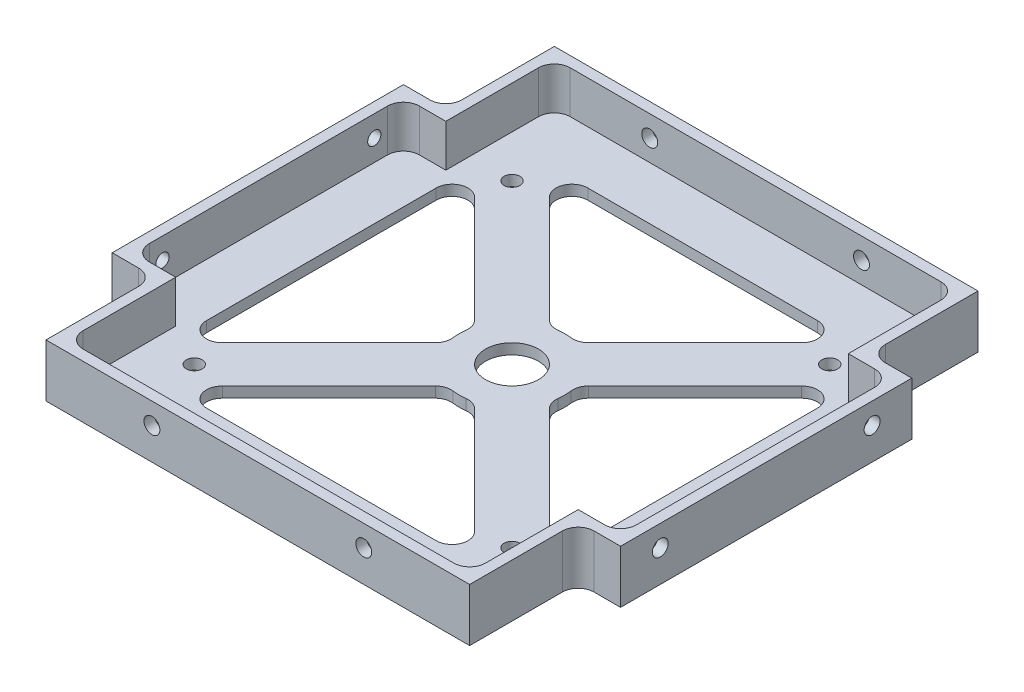
SolidWorks part; units mm, degrees
material "6061-T6 (SS)"
ref_plane "Front Plane" through (0, 0, 0) normal (0, 0, 1) x (1, 0, 0)
ref_plane "Top Plane" through (0, 0, 0) normal (0, 1, 0) x (1, 0, 0)
ref_plane "Right Plane" through (0, 0, 0) normal (1, 0, 0) x (0, 0, -1)
sketch "Sketch1" plane through (0, 0, 0) normal (0, 1, 0) x (1, 0, 0)
  line L0 (0, 8) -> (8, 0)
  line L1 (0, 0) -> (96, 0)
  line L2 (0, 0) -> (0, 96)
  line L3 (0, 96) -> (96, 96)
  line L4 (96, 0) -> (96, 96)
  line L5 (48, 96) -> (48, 0) construction
  line L6 (0, 48) -> (96, 48) construction
  line L7 (96, 8) -> (88, 0)
  line L8 (96, 88) -> (88, 96)
  line L9 (0, 88) -> (8, 96)
  dimension "D1" = 96
  dimension "D2" = 96
  dimension "D3" = 8
  dimension "D4" = 8
extrude "Boss-Extrude1" add sketch "Sketch1" along normal blind 10 contours L9 L2 L0 L1 L7 L4 L8 L3
sketch "Sketch2" plane through (0, 0, 0) normal (0, -1, 0) x (-1, 0, 0)
  line L0 (-4, 92) -> (-92, 4) construction
  line L1 (0, 88) -> (-8, 96) construction
  line L2 (-96, 8) -> (-88, 0) construction
  line L3 (-92, 92) -> (-4, 4) construction
  line L4 (-96, 88) -> (-88, 96) construction
  line L5 (0, 8) -> (-8, 0) construction
  line L6 (-12, 84) -> (-84, 84) construction
  line L7 (-84, 84) -> (-84, 12) construction
  line L8 (-84, 12) -> (-12, 12) construction
  line L9 (-12, 12) -> (-12, 84) construction
  line L10 (-8, 96) -> (-88, 96) construction
  line L12 (-19.0711, 84) -> (-84, 19.0711)
  line L13 (-12, 76.9289) -> (-76.9289, 12)
  line L14 (-12, 19.0711) -> (-76.9289, 84)
  line L15 (-19.0711, 12) -> (-84, 76.9289)
  line L16 (-12, 76.9289) -> (-12, 19.0711)
  line L17 (-19.0711, 12) -> (-76.9289, 12)
  line L18 (-84, 19.0711) -> (-84, 76.9289)
  line L19 (-76.9289, 84) -> (-19.0711, 84)
  circle A0 centre (-48, 48) radius 10
  circle A1 centre (-48, 48) radius 5
  dimension "D6" = 20
  dimension "D7" = 10
  dimension "D1" = 12
  dimension "D2" = 10
  dimension "D3" = 5
  dimension "D4" = 10
  dimension "D5" = 5
extrude "Cut-Extrude1" cut sketch "Sketch2" against normal through all contours A0 L12 L19 L14 | A0 L14 L16 L13 | A0 L13 L17 L15 | A0 L15 L18 L12 | A1
fillet "Fillet1" radius 3 16 edges at (19.0711, 5, -12) (76.9289, 5, -12) (50.5882, 5, -38.3407) (38.3407, 5, -50.5882) (45.4118, 5, -38.3407) (57.6593, 5, -50.5882) (12, 5, -19.0711) (38.3407, 5, -45.4118) (50.5882, 5, -57.6593) (84, 5, -19.0711) (84, 5, -76.9289) (57.6593, 5, -45.4118) (45.4118, 5, -57.6593) (76.9289, 5, -84) (19.0711, 5, -84) (12, 5, -76.9289)
sketch "Sketch5" plane through (0, 10, 0) normal (0, 1, 0) x (1, 0, 0)
  line L0 (8, 0) -> (8, 20.5)
  line L3 (0, 8) -> (8, 0)
  line L4 (0, 8) -> (0, 20.5)
  line L5 (0, 8) -> (0, 88) construction
  line L6 (0, 20.5) -> (8, 20.5)
  line L7 (0, 48) -> (96, 48) construction
  line L8 (96, 8) -> (96, 88) construction
  line L9 (48, 96) -> (48, 0) construction
  line L10 (8, 96) -> (88, 96) construction
  line L11 (8, 0) -> (88, 0) construction
  line L12 (96, 8) -> (88, 0)
  line L13 (96, 8) -> (96, 20.5)
  line L14 (96, 20.5) -> (88, 20.5)
  line L15 (88, 0) -> (88, 20.5)
  line L16 (96, 75.5) -> (88, 75.5)
  line L17 (96, 88) -> (96, 75.5)
  line L18 (96, 88) -> (88, 96)
  line L19 (88, 96) -> (88, 75.5)
  line L20 (8, 96) -> (8, 75.5)
  line L21 (0, 88) -> (8, 96)
  line L22 (0, 88) -> (0, 75.5)
  line L23 (0, 75.5) -> (8, 75.5)
  dimension "D1" = 20.5
extrude "Cut-Extrude4" cut sketch "Sketch5" against normal through all
sketch "Sketch6" plane through (0, 10, 0) normal (0, 1, 0) x (1, 0, 0)
  line L90 (86, 73.5) -> (86, 94)
  line L91 (94, 73.5) -> (86, 73.5)
  line L92 (94, 22.5) -> (94, 73.5)
  line L93 (86, 22.5) -> (94, 22.5)
  line L94 (86, 2) -> (86, 22.5)
  line L95 (10, 2) -> (86, 2)
  line L96 (10, 22.5) -> (10, 2)
  line L97 (2, 22.5) -> (10, 22.5)
  line L98 (2, 73.5) -> (2, 22.5)
  line L99 (10, 73.5) -> (2, 73.5)
  line L100 (10, 94) -> (10, 73.5)
  line L101 (86, 94) -> (10, 94)
  line L102 (86, 73.5) -> (86, 94)
  line L103 (94, 73.5) -> (86, 73.5)
  line L104 (94, 22.5) -> (94, 73.5)
  line L105 (86, 22.5) -> (94, 22.5)
  line L106 (86, 2) -> (86, 22.5)
  line L107 (10, 2) -> (86, 2)
  line L108 (10, 22.5) -> (10, 2)
  line L109 (2, 22.5) -> (10, 22.5)
  line L110 (2, 73.5) -> (2, 22.5)
  line L111 (10, 73.5) -> (2, 73.5)
  line L112 (10, 94) -> (10, 73.5)
  line L113 (86, 94) -> (10, 94)
  dimension "D1" = 2
extrude "Cut-Extrude5" cut sketch "Sketch6" against normal blind 8
fillet "Fillet2" radius 3 12 edges at (88, 5, -75.5) (88, 5, -20.5) (8, 5, -75.5) (8, 5, -20.5) (86, 6, -94) (94, 6, -73.5) (94, 6, -22.5) (86, 6, -2) (10, 6, -94) (10, 6, -2) (2, 6, -22.5) (2, 6, -73.5)
sketch "Sketch7" plane through (0, 0, 0) normal (0, -1, 0) x (1, 0, 0)
  line L0 (78, -18) -> (18, -18) construction
  line L1 (78, -78) -> (18, -78)
  line L2 (78, -78) -> (78, -18)
  line L3 (78, -18) -> (18, -18)
  line L4 (18, -78) -> (18, -18)
  line L5 (78, -78) -> (18, -18) construction
  line L6 (78, -18) -> (18, -78) construction
  line L7 (78, -18) -> (78, -78) construction
  line L8 (8, 0) -> (88, 0) construction
  line L9 (96, -20.5) -> (96, -75.5) construction
  line L10 (88, -96) -> (88, -78.5) construction
  circle A0 centre (78, -18) radius 1.5
  circle A1 centre (18, -18) radius 1.5
  circle A2 centre (18, -78) radius 1.5
  circle A3 centre (78, -78) radius 1.5
  point P0 (48, -48)
  dimension "D1" = 2
  dimension "D5" = 3
  dimension "D8" = 10
  dimension "D2" = 60
  dimension "D3" = 60
  dimension "D6" = 18
  dimension "D7" = 18
  dimension "D4" = 2
sketch "Sketch8" plane through (0, 0, 0) normal (0, 0, 1) x (1, 0, 0)
  line L0 (8, 6) -> (88, 6) construction
  line L1 (8, 10) -> (8, 0) construction
  line L2 (88, 10) -> (88, 0) construction
  line L3 (8, 0) -> (88, 0) construction
  line L4 (48, 10) -> (48, 0) construction
  line L5 (8, 10) -> (88, 10) construction
  dimension "D1" = 6
sketch "Sketch9" plane through (0, 0, 0) normal (-1, 0, 0) x (0, 0, 1)
  line L0 (-75.5, 6) -> (-20.5, 6) construction
  line L1 (-75.5, 0) -> (-75.5, 10) construction
  line L2 (-20.5, 0) -> (-20.5, 10) construction
  line L3 (-20.5, 0) -> (-75.5, 0) construction
  line L4 (-48, 10) -> (-48, 0) construction
  line L5 (-20.5, 10) -> (-75.5, 10) construction
  dimension "D1" = 6
hole_wizard "Ø3.0mm Dowel Hole1" positions "Sketch12" profile "Sketch13" hole size "Ø3.0" standard "ANSI Metric"
sketch "Sketch12" plane through (0, 0, 0) normal (0, 0, 1) x (1, 0, 0)
  line L0 (8, 6) -> (88, 6) construction
  line L2 (48, 10) -> (48, 0) construction
  point P0 (28, 6)
  point P4 (68, 6)
  dimension "D1" = 40
  dimension "D2" = 20
sketch "Sketch13" plane through (28, 6, 0) normal (1, 0, 0) x (0, -1, 0)
  line L0 (0, 0) -> (0, 8.4013)
  line L1 (0, 8.4013) -> (1.5, 7.5)
  line L2 (1.5, 7.5) -> (1.5, 0)
  line L5 (1.5, 0) -> (0, 0)
  line L10 (0, 8.4013) -> (-1.5, 7.5) construction
  line L11 (0, -6.35) -> (0, 107.95) construction
  dimension "Hole Dia." = 3
  dimension "Hole Depth" = 7.5
  dimension "Drill Angle" = 118
hole_wizard "Tap Drill for M3x0.5 Tap1" positions "Sketch14" profile "Sketch15" hole size "M3x0.5" standard "ANSI Metric" end condition up to next
sketch "Sketch14" plane through (0, 0, 0) normal (-1, 0, 0) x (0, 0, 1)
  line L0 (-75.5, 6) -> (-20.5, 6) construction
  line L1 (-48, 10) -> (-48, 0) construction
  point P0 (-68, 6)
  point P4 (-28, 6)
  dimension "D1" = 40
  dimension "D2" = 20
sketch "Sketch15" plane through (0, 6, -68) normal (0, 1, 0) x (0, 0, 1)
  line L0 (0, 0) -> (0, 2)
  line L1 (0, 2) -> (1.25, 2)
  line L2 (1.25, 2) -> (1.25, 0)
  line L5 (1.25, 0) -> (0, 0)
  line L11 (0, -6.35) -> (0, 107.95) construction
  dimension "Thru Hole Dia." = 2.5
  dimension "Thru Hole Depth" = 2
ref_plane "Plane1" through (48, 0, 0) normal (-1, 0, 0) x (0, 0, 1)
ref_plane "Plane2" through (0, 0, -48) normal (0, 0, 1) x (1, 0, 0)
mirror "Mirror1" about plane through (0, 0, -48) normal (0, 0, 1) of "Ø3.0mm Dowel Hole1"
sketch "Sketch16" plane through (0, 0, 0) normal (-1, 0, 0) x (0, 0, 1)
  line L0 (-48, 0) -> (-48, 10) construction
  line L1 (-20.5, 0) -> (-75.5, 0) construction
  line L2 (-20.5, 10) -> (-75.5, 10) construction
  line L4 (-40.9661, 4.5188) -> (-54.475, 4.5188) construction
hole_wizard "Ø3.0mm Dowel Hole3" positions "3DSketch1" profile "Sketch17" hole size "Ø3.0" standard "ANSI Metric" end condition through all
sketch3d "3DSketch1"
  point P0 (78, 0, -18)
  point P3 (78, 0, -78)
  point P6 (18, 0, -78)
  point P9 (18, 0, -18)
sketch "Sketch17" plane through (78, 0, -18) normal (1, 0, 0) x (0, 0, -1)
  line L0 (0, 0) -> (0, 10)
  line L1 (0, 10) -> (1.5, 10)
  line L2 (1.5, 10) -> (1.5, 0)
  line L5 (1.5, 0) -> (0, 0)
  line L11 (0, -6.35) -> (0, 107.95) construction
  dimension "Thru Hole Dia." = 3
  dimension "Thru Hole Depth" = 10
sketch "Sketch18" plane through (96, 0, 0) normal (1, 0, 0) x (0, 0, -1)
  line L1 (20.5, 0) -> (75.5, 0) construction
  line L4 (75.5, 0) -> (75.5, 10) construction
  point P8 (28, 6)
  point P9 (68, 6)
  dimension "D1" = 7.5
  dimension "D2" = 6
  dimension "D3" = 40
  dimension "D4" = 6
hole_wizard "Ø3.0mm Dowel Hole4" positions "3DSketch2" profile "Sketch19" hole size "Ø3.0" standard "ANSI Metric" end condition up to next
sketch3d "3DSketch2"
  point P0 (96, 6, -68)
  point P3 (96, 6, -28)
sketch "Sketch19" plane through (96, 6, -68) normal (0, 1, 0) x (0, 0, -1)
  line L0 (0, 0) -> (0, 2)
  line L1 (0, 2) -> (1.5, 2)
  line L2 (1.5, 2) -> (1.5, 0)
  line L5 (1.5, 0) -> (0, 0)
  line L11 (0, -6.35) -> (0, 107.95) construction
  dimension "Thru Hole Dia." = 3
  dimension "Thru Hole Depth" = 2
